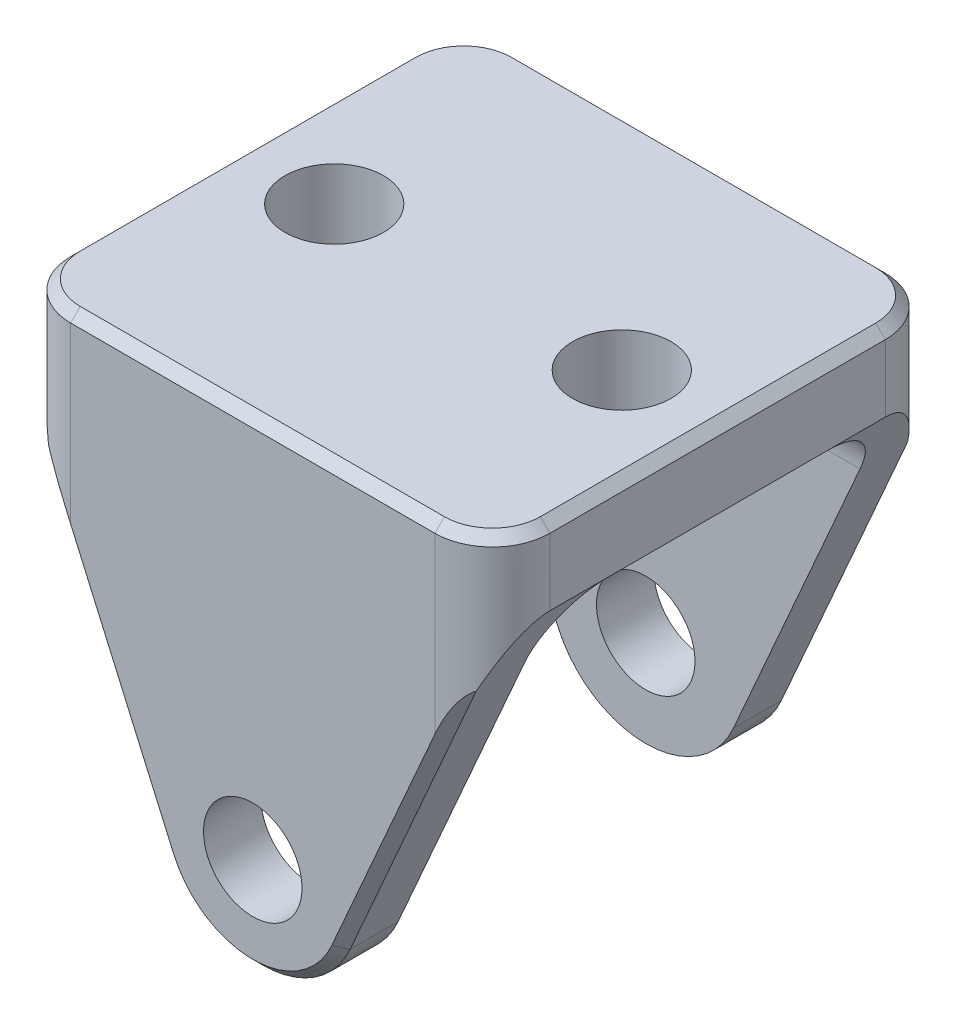
SolidWorks part; units mm, degrees
material "6061-T6 (SS)"
ref_plane "Front Plane" through (0, 0, 0) normal (0, 0, 1) x (1, 0, 0)
ref_plane "Top Plane" through (0, 0, 0) normal (0, 1, 0) x (1, 0, 0)
ref_plane "Right Plane" through (0, 0, 0) normal (1, 0, 0) x (0, 0, -1)
ref_plane "A-Arm Plane" through (0, 0, 291.592) normal (0, 0, 1) x (1, 0, 0)
sketch "Sketch1" plane through (0, 0, 291.592) normal (0, 0, 1) x (1, 0, 0)
  line L0 (9.4274, 518.1433) -> (-0.635, 541.02)
  line L1 (-0.635, 541.02) -> (-0.635, 546.1)
  line L2 (-0.635, 546.1) -> (31.115, 546.1)
  line L3 (31.115, 546.1) -> (31.115, 541.02)
  line L4 (31.115, 541.02) -> (21.0526, 518.1433)
  line L5 (15.24, 520.7) -> (15.24, 546.1) construction
  line L7 (24.765, 541.02) -> (24.765, 546.1) construction
  line L10 (21.59, 541.02) -> (27.94, 541.02) construction
  line L11 (21.59, 541.02) -> (21.59, 530.86) construction
  line L12 (21.59, 530.86) -> (27.94, 530.86) construction
  line L13 (27.94, 541.02) -> (27.94, 530.86) construction
  circle A1 centre (15.24, 520.7) radius 11.1125 construction
  arc A2 (9.4274, 518.1433) -> (21.0526, 518.1433) centre (15.24, 520.7) ccw
  dimension "D1" = 22.225
  dimension "D2" = 6.35
  dimension "D3" = 5.08
  dimension "D4" = 6.35
  dimension "D5" = 10.16
  dimension "D6" = 6.35
  dimension "D7" = 31.75
  dimension "D8" = 25.4
ref_plane "Plane2" through (0, 546.1, 0) normal (0, -1, 0) x (1, 0, 0)
sketch "Arm Thickness + Clearance" plane through (0, 546.1, 0) normal (0, -1, 0) x (1, 0, 0)
  line L0 (-0.635, 302.7045) -> (-0.635, 306.5145)
  line L1 (-0.635, 302.7045) -> (31.115, 302.7045) construction
  line L2 (-0.635, 302.7045) -> (-0.635, 280.4795)
  line L3 (-0.635, 280.4795) -> (31.115, 280.4795) construction
  line L4 (31.115, 302.7045) -> (31.115, 280.4795)
  line L5 (-0.635, 306.5145) -> (31.115, 306.5145)
  line L6 (31.115, 306.5145) -> (31.115, 302.7045)
  line L7 (31.115, 280.4795) -> (31.115, 276.6695)
  line L8 (31.115, 276.6695) -> (-0.635, 276.6695)
  line L9 (-0.635, 276.6695) -> (-0.635, 280.4795)
  point P4 (-0.635, 291.592)
  point P5 (31.115, 291.592)
  dimension "D1" = 22.225
  dimension "D2" = 3.81
extrude "Bulk Triangle" add sketch "Sketch1" along normal up to vertex (14.9225 mm away) and the other way up to vertex (14.9225 mm away) up to point (-0.635, 546.1, 306.5145) other way up to point (-0.635, 546.1, 276.6695)
ref_plane "Plane3" through (15.24, 0, 0) normal (1, 0, 0) x (0, 0, -1)
sketch "Sketch3" plane through (15.24, 0, 0) normal (1, 0, 0) x (0, 0, -1)
  line L0 (-306.5379, 541.0068) -> (-276.6929, 541.0081) construction
  line L1 (-306.5379, 541.0068) -> (-276.6929, 541.0081) construction
  line L3 (-276.6917, 514.3381) -> (-276.6919, 518.1314) construction
  line L6 (-276.6917, 514.3381) -> (-276.6919, 518.1314) construction
  line L7 (-306.5369, 518.1301) -> (-306.5367, 514.3368) construction
  line L8 (-306.5369, 518.1301) -> (-306.5367, 514.3368) construction
  line L9 (-306.5367, 514.3368) -> (-276.6917, 514.3381)
  line L16 (-302.7279, 541.0069) -> (-302.7267, 514.3369)
  line L17 (-302.7281, 546.0869) -> (-280.5031, 546.0879) construction
  line L18 (-302.7281, 546.0869) -> (-280.5031, 546.0879) construction
  line L19 (-302.7267, 514.3369) -> (-280.5017, 514.3379)
  line L20 (-280.5017, 514.3379) -> (-280.5029, 541.0079)
  line L21 (-280.5029, 541.0079) -> (-302.7279, 541.0069)
extrude "U-Cutout" cut sketch "Sketch3" against normal through all both and the other way through all contours L20 L21 L16 L19
hole_wizard "1/4 Clearance Hole1" positions "3DSketch1" profile "Sketch7" hole size "1/4" standard "ANSI Inch" end condition through all
sketch3d "3DSketch1"
  arc A0 (9.4274, 518.1433, 306.5145) -> (21.0526, 518.1433, 306.5145) centre (15.24, 520.7, 306.5145) ccw construction
  arc A1 (9.4274, 518.1433, 306.5145) -> (21.0526, 518.1433, 306.5145) centre (15.24, 520.7, 306.5145) ccw
  point P0 (15.24, 520.7, 306.5145)
  point P6 (15.24, 520.7, 312.8645)
  point P7 (15.24, 520.7, 312.8645)
sketch "Sketch7" plane through (15.24, 520.7, 306.5145) normal (1, 0, 0) x (0, -1, 0)
  line L0 (0, 0) -> (0, 29.845)
  line L1 (0, 29.845) -> (3.2639, 29.845)
  line L2 (3.2639, 29.845) -> (3.2639, 0)
  line L5 (3.2639, 0) -> (0, 0)
  line L11 (0, -6.35) -> (0, 107.95) construction
  dimension "Thru Hole Dia." = 6.5278
  dimension "Thru Hole Depth" = 29.845
hole_wizard "1/4 Clearance Hole2" positions "3DSketch2" profile "Sketch8" hole size "1/4" standard "ANSI Inch"
sketch3d "3DSketch2"
  line L0 (5.715, 541.02, 291.592) -> (24.765, 541.02, 291.592) construction
  line L4 (15.24, 541.02, 302.7045) -> (15.24, 541.02, 280.4795) construction
  line L5 (-0.635, 541.02, 302.7045) -> (31.115, 541.02, 302.7045) construction
  line L6 (-0.635, 541.02, 280.4795) -> (31.115, 541.02, 280.4795) construction
  line L8 (31.115, 541.02, 302.7045) -> (31.115, 541.02, 280.4795) construction
  point P0 (24.765, 541.02, 291.592)
  point P2 (5.715, 541.02, 291.592)
  point P20 (15.24, 541.02, 291.592)
  dimension "D1" = 6.35
sketch "Sketch8" plane through (24.765, 541.02, 291.592) normal (1, 0, 0) x (0, 0, -1)
  line L0 (0, 0) -> (0, 5.08)
  line L1 (0, 5.08) -> (3.2639, 5.08)
  line L2 (3.2639, 5.08) -> (3.2639, 0)
  line L5 (3.2639, 0) -> (0, 0)
  line L11 (0, -6.35) -> (0, 107.95) construction
  dimension "Thru Hole Dia." = 6.5278
  dimension "Thru Hole Depth" = 5.08
fillet "Inner Fillet" radius 3.81 2 edges at (15.24, 541.02, 280.4795) (15.24, 541.02, 302.7045)
chamfer "Triangle Deburr" distance 0.635 angle 45 6 edges at (4.3962, 529.5817, 276.6695) (15.24, 514.35, 276.6695) (26.0838, 529.5817, 276.6695) (4.3962, 529.5817, 306.5145) (15.24, 514.35, 306.5145) (26.0838, 529.5817, 306.5145)
fillet "Outer Fillet" radius 3.81 4 edges at (-0.635, 544.3486, 276.6695) (31.115, 544.3486, 276.6695) (-0.635, 544.3486, 306.5145) (31.115, 544.3486, 306.5145)
chamfer "Clamp Face Deburr" distance 0.635 angle 45 8 edges at (-0.635, 546.1, 291.592) (0.4809, 546.1, 305.3986) (0.4809, 546.1, 277.7854) (15.24, 546.1, 306.5145) (15.24, 546.1, 276.6695) (29.9991, 546.1, 305.3986) (29.9991, 546.1, 277.7854) (31.115, 546.1, 291.592)
